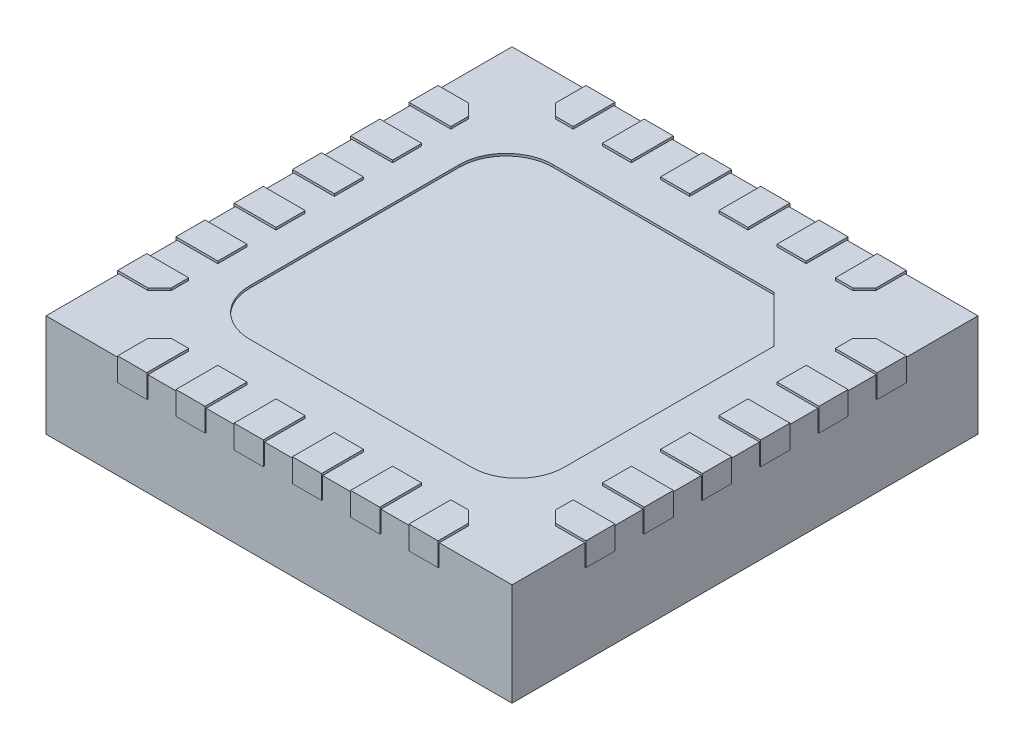
SolidWorks part; units mm, degrees
ref_plane "Front Plane" through (0, 0, 0) normal (0, 0, 1) x (1, 0, 0)
ref_plane "Top Plane" through (0, 0, 0) normal (0, 1, 0) x (1, 0, 0)
ref_plane "Right Plane" through (0, 0, 0) normal (1, 0, 0) x (0, 0, -1)
sketch "Sketch1" plane through (0, 0, 0) normal (0, 1, 0) x (1, 0, 0)
  line L1 (-2, 2) -> (2, 2)
  line L2 (-2, 2) -> (-2, -2)
  line L3 (-2, -2) -> (2, -2)
  line L4 (2, 2) -> (2, -2)
  dimension "D1" = 4
  dimension "D2" = 4
  dimension "D3" = 2
  dimension "D4" = 2
extrude "Boss-Extrude1" add sketch "Sketch1" along normal blind 0.88
sketch "Sketch2" plane through (0, 0.88, 0) normal (0, 1, 0) x (1, 0, 0)
  line L0 (2, -2) -> (2, 2) construction
  line L1 (2, 1.375) -> (1.75, 1.375)
  line L3 (2, 1.125) -> (1.65, 1.125)
  line L4 (1.65, 1.275) -> (1.65, 1.125)
  line L5 (2, 0.625) -> (1.65, 0.625)
  line L6 (1.65, 0.875) -> (1.65, 0.625)
  line L7 (2, 0.875) -> (1.65, 0.875)
  line L9 (2, 0.125) -> (1.65, 0.125)
  line L10 (1.65, 0.375) -> (1.65, 0.125)
  line L11 (2, 0.375) -> (1.65, 0.375)
  line L13 (2, -0.375) -> (1.65, -0.375)
  line L14 (1.65, -0.125) -> (1.65, -0.375)
  line L15 (2, -0.125) -> (1.65, -0.125)
  line L17 (2, -0.875) -> (1.65, -0.875)
  line L18 (1.65, -0.625) -> (1.65, -0.875)
  line L19 (2, -0.625) -> (1.65, -0.625)
  line L21 (2, -1.375) -> (1.75, -1.375)
  line L22 (1.65, -1.125) -> (1.65, -1.275)
  line L23 (2, -1.125) -> (1.65, -1.125)
  line L25 (0, 2) -> (0, -2) construction
  line L26 (2, 2) -> (-2, 2) construction
  line L27 (-2, -2) -> (2, -2) construction
  line L28 (-2, 0) -> (2, 0) construction
  line L29 (-2, 2) -> (-2, -2) construction
  line L30 (-1.375, -2) -> (-1.375, -2.01)
  line L31 (-2, -1.125) -> (-1.65, -1.125)
  line L32 (-1.65, -1.125) -> (-1.65, -1.275)
  line L33 (-2, -1.375) -> (-1.75, -1.375)
  line L34 (-1.375, -2.01) -> (-1.125, -2.01)
  line L35 (-2, -0.625) -> (-1.65, -0.625)
  line L36 (-1.65, -0.625) -> (-1.65, -0.875)
  line L37 (-2, -0.875) -> (-1.65, -0.875)
  line L38 (1.375, -2.01) -> (1.375, -2)
  line L39 (-2, -0.125) -> (-1.65, -0.125)
  line L40 (-1.65, -0.125) -> (-1.65, -0.375)
  line L41 (-2, -0.375) -> (-1.65, -0.375)
  line L42 (-2.01, -0.125) -> (-2.01, -0.375)
  line L43 (-2, 0.375) -> (-1.65, 0.375)
  line L44 (-1.65, 0.375) -> (-1.65, 0.125)
  line L45 (-2, 0.125) -> (-1.65, 0.125)
  line L46 (-2.01, 0.375) -> (-2.01, 0.125)
  line L47 (-2, 0.875) -> (-1.65, 0.875)
  line L48 (-1.65, 0.875) -> (-1.65, 0.625)
  line L49 (-2, 0.625) -> (-1.65, 0.625)
  line L50 (-1.65, 1.275) -> (-1.65, 1.125)
  line L51 (-2, 1.125) -> (-1.65, 1.125)
  line L52 (-2.01, 0.875) -> (-2.01, 0.625)
  line L53 (-2, 1.375) -> (-1.75, 1.375)
  line L54 (-1.375, -1.75) -> (-1.375, -2)
  line L55 (-1.275, -1.65) -> (-1.125, -1.65)
  line L56 (-1.125, -1.65) -> (-1.125, -2)
  line L57 (1.125, 2.01) -> (1.125, 2)
  line L58 (-0.875, -1.65) -> (-0.875, -2)
  line L59 (-0.875, -1.65) -> (-0.625, -1.65)
  line L60 (-0.625, -1.65) -> (-0.625, -2)
  line L61 (-0.875, -2.01) -> (-0.625, -2.01)
  line L62 (-0.375, -1.65) -> (-0.375, -2)
  line L63 (-0.375, -1.65) -> (-0.125, -1.65)
  line L64 (-0.125, -1.65) -> (-0.125, -2)
  line L65 (-0.375, -2.01) -> (-0.125, -2.01)
  line L66 (0.125, -1.65) -> (0.125, -2)
  line L67 (0.125, -1.65) -> (0.375, -1.65)
  line L68 (0.375, -1.65) -> (0.375, -2)
  line L69 (0.125, -2.01) -> (0.375, -2.01)
  line L70 (0.625, -1.65) -> (0.625, -2)
  line L71 (0.625, -1.65) -> (0.875, -1.65)
  line L72 (0.875, -1.65) -> (0.875, -2)
  line L73 (0.625, -2.01) -> (0.875, -2.01)
  line L74 (1.125, -1.65) -> (1.125, -2)
  line L75 (1.125, -1.65) -> (1.275, -1.65)
  line L76 (1.375, -1.75) -> (1.375, -2)
  line L77 (1.125, -2.01) -> (1.375, -2.01)
  line L79 (1.375, 1.75) -> (1.375, 2)
  line L80 (1.125, 1.65) -> (1.275, 1.65)
  line L81 (1.125, 1.65) -> (1.125, 2)
  line L83 (0.875, 1.65) -> (0.875, 2)
  line L84 (0.625, 1.65) -> (0.875, 1.65)
  line L85 (0.625, 1.65) -> (0.625, 2)
  line L87 (0.375, 1.65) -> (0.375, 2)
  line L88 (0.125, 1.65) -> (0.375, 1.65)
  line L89 (0.125, 1.65) -> (0.125, 2)
  line L91 (-0.125, 1.65) -> (-0.125, 2)
  line L92 (-0.375, 1.65) -> (-0.125, 1.65)
  line L93 (-0.375, 1.65) -> (-0.375, 2)
  line L95 (-0.625, 1.65) -> (-0.625, 2)
  line L96 (-0.875, 1.65) -> (-0.625, 1.65)
  line L97 (-0.875, 1.65) -> (-0.875, 2)
  line L99 (-1.125, 1.65) -> (-1.125, 2)
  line L100 (-1.275, 1.65) -> (-1.125, 1.65)
  line L101 (-1.375, 1.75) -> (-1.375, 2)
  line L102 (-1.65, -1.275) -> (-1.75, -1.375)
  line L103 (-1.275, -1.65) -> (-1.375, -1.75)
  line L104 (-1.75, 1.375) -> (-1.65, 1.275)
  line L105 (-1.375, 1.75) -> (-1.275, 1.65)
  line L106 (1.375, 1.75) -> (1.275, 1.65)
  line L107 (1.75, 1.375) -> (1.65, 1.275)
  line L108 (1.275, -1.65) -> (1.375, -1.75)
  line L109 (1.65, -1.275) -> (1.75, -1.375)
  line L110 (-2, 1.375) -> (-2.01, 1.375)
  line L111 (-2.01, 1.375) -> (-2.01, 1.125)
  line L112 (-2.01, 1.125) -> (-2, 1.125)
  line L113 (-2.01, -1.375) -> (-2, -1.375)
  line L114 (-2, -1.125) -> (-2.01, -1.125)
  line L115 (-2.01, -0.875) -> (-2, -0.875)
  line L116 (-2, -0.875) -> (-1.9998, -0.875)
  line L117 (-2.01, -0.625) -> (-2, -0.625)
  line L118 (-2.01, -1.125) -> (-2.01, -1.375)
  line L119 (-2, -0.375) -> (-2.01, -0.375)
  line L120 (-2.01, -0.625) -> (-2.01, -0.875)
  line L121 (-2.01, -0.125) -> (-2, -0.125)
  line L122 (-2.01, 0.125) -> (-2, 0.125)
  line L123 (-2.01, 0.375) -> (-2, 0.375)
  line L124 (-2, 0.375) -> (-1.9995, 0.375)
  line L125 (-2.01, 0.625) -> (-2, 0.625)
  line L126 (-2.01, 0.875) -> (-2, 0.875)
  line L127 (-1.125, -2) -> (-1.125, -2.01)
  line L128 (-0.875, -2.01) -> (-0.875, -2)
  line L129 (-0.625, -2.01) -> (-0.625, -2)
  line L130 (-0.375, -2.01) -> (-0.375, -2)
  line L131 (-0.125, -2) -> (-0.125, -2.01)
  line L132 (0.125, -2.01) -> (0.125, -2)
  line L133 (0.375, -2.01) -> (0.375, -2)
  line L134 (0.625, -2.01) -> (0.625, -2)
  line L135 (0.875, -2.01) -> (0.875, -2)
  line L136 (1.125, -2.01) -> (1.125, -2)
  line L137 (0.875, 2.01) -> (0.875, 2)
  line L143 (0.625, 2.01) -> (0.625, 2)
  line L144 (0.375, 2.01) -> (0.375, 2)
  line L145 (0.125, 2.01) -> (0.125, 2)
  line L146 (-0.125, 2) -> (-0.125, 2.01)
  line L147 (-0.375, 2.01) -> (-0.375, 2)
  line L148 (-0.625, 2.01) -> (-0.625, 2)
  line L149 (-0.875, 2.01) -> (-0.875, 2)
  line L150 (-1.125, 2) -> (-1.125, 2.01)
  line L151 (1.125, 2.01) -> (1.375, 2.01)
  line L152 (0.625, 2.01) -> (0.875, 2.01)
  line L153 (0.125, 2.01) -> (0.375, 2.01)
  line L154 (-0.375, 2.01) -> (-0.125, 2.01)
  line L155 (-0.875, 2.01) -> (-0.625, 2.01)
  line L156 (1.375, 2.01) -> (1.375, 2)
  line L157 (-1.375, 2.01) -> (-1.125, 2.01)
  line L158 (-1.375, 2) -> (-1.375, 2.01)
  line L159 (2.01, 0.875) -> (2, 0.875)
  line L160 (2.01, 0.625) -> (2, 0.625)
  line L161 (2, 0.375) -> (1.9995, 0.375)
  line L162 (2.01, 0.375) -> (2, 0.375)
  line L163 (2.01, 0.125) -> (2, 0.125)
  line L164 (2.01, -0.125) -> (2, -0.125)
  line L165 (2.01, -0.625) -> (2.01, -0.875)
  line L166 (2, -0.375) -> (2.01, -0.375)
  line L167 (2.01, -1.125) -> (2.01, -1.375)
  line L168 (2.01, -0.625) -> (2, -0.625)
  line L169 (2, -0.875) -> (1.9998, -0.875)
  line L170 (2.01, -0.875) -> (2, -0.875)
  line L171 (2, -1.125) -> (2.01, -1.125)
  line L172 (2.01, -1.375) -> (2, -1.375)
  line L173 (2.01, 1.125) -> (2, 1.125)
  line L174 (2.01, 1.375) -> (2.01, 1.125)
  line L175 (2, 1.375) -> (2.01, 1.375)
  line L176 (2.01, 0.875) -> (2.01, 0.625)
  line L177 (2.01, 0.375) -> (2.01, 0.125)
  line L178 (2.01, -0.125) -> (2.01, -0.375)
  dimension "D1" = 0.01
  dimension "D2" = 0.01
  dimension "D4" = 0.125
  dimension "D6" = 0.25
  dimension "D8" = 0.125
  dimension "D3" = 6
  dimension "D7" = 6
extrude "Boss-Extrude3" add sketch "Sketch2" along normal blind 0.02 and the other way blind 0.18 contours L51 L50 L104 L53 L110 L111 L112 | L47 L48 L49 L125 L52 L126 | L43 L44 L45 L122 L46 L123 | L41 L40 L39 L121 L42 L119 | L115 L120 L117 L35 L36 L37 | L33 L102 L32 L31 L114 L118 L113 | L103 L54 L30 L34 L127 L56 L55 | L59 L60 L129 L61 L128 L58 | L63 L64 L131 L65 L130 L62 | L67 L68 L133 L69 L132 L66 | L71 L72 L135 L73 L134 L70 | L75 L108 L76 L38 L77 L136 L74 | L21 L109 L22 L23 L171 L167 L172 | L170 L165 L168 L19 L18 L17 | L13 L14 L15 L164 L178 L166 | L162 L177 L163 L9 L10 L11 | L5 L6 L7 L159 L176 L160 | L3 L4 L107 L1 L175 L174 L173 | L80 L106 L79 L156 L151 L57 L81 | L84 L83 L137 L152 L143 L85 | L88 L87 L144 L153 L145 L89 | L92 L91 L146 L154 L147 L93 | L96 L95 L148 L155 L149 L97 | L105 L100 L99 L150 L157 L158 L101
sketch "Sketch3" plane through (0, 0.88, 0) normal (0, 1, 0) x (1, 0, 0)
  line L0 (0.95, 1.3) -> (1.35, 0.9)
  line L1 (-0.95, 1.3) -> (0.95, 1.3)
  line L2 (-1.35, 0.9) -> (-1.35, -0.9)
  line L3 (-0.95, -1.3) -> (0.95, -1.3)
  line L4 (1.35, 0.9) -> (1.35, -0.9)
  arc A0 (0.95, -1.3) -> (1.35, -0.9) centre (0.95, -0.9) ccw
  arc A1 (-0.95, -1.3) -> (-1.35, -0.9) centre (-0.95, -0.9) cw
  arc A2 (-0.95, 1.3) -> (-1.35, 0.9) centre (-0.95, 0.9) ccw
  point P3 (1.35, 1.3)
  point P7 (1.35, -1.3)
  point P10 (-1.35, -1.3)
  point P13 (-1.35, 1.3)
  dimension "D5" = 0.4
  dimension "D1" = 2.7
  dimension "D2" = 2.6
  dimension "D3" = 1.35
  dimension "D4" = 1.3
extrude "Cut-Extrude1" cut sketch "Sketch3" against normal blind 0.02
sketch "Sketch4" plane through (0, 0, 0) normal (0, -1, 0) x (1, 0, 0)
  line L0 (2, 2) -> (2, -2) construction
  line L1 (2, -2) -> (-2, -2) construction
  circle A0 centre (1.5, -1.5) radius 0.1
  dimension "D1" = 0.2
  dimension "D2" = 0.5
  dimension "D3" = 0.5
extrude "Cut-Extrude2" cut sketch "Sketch4" against normal blind 0.02
